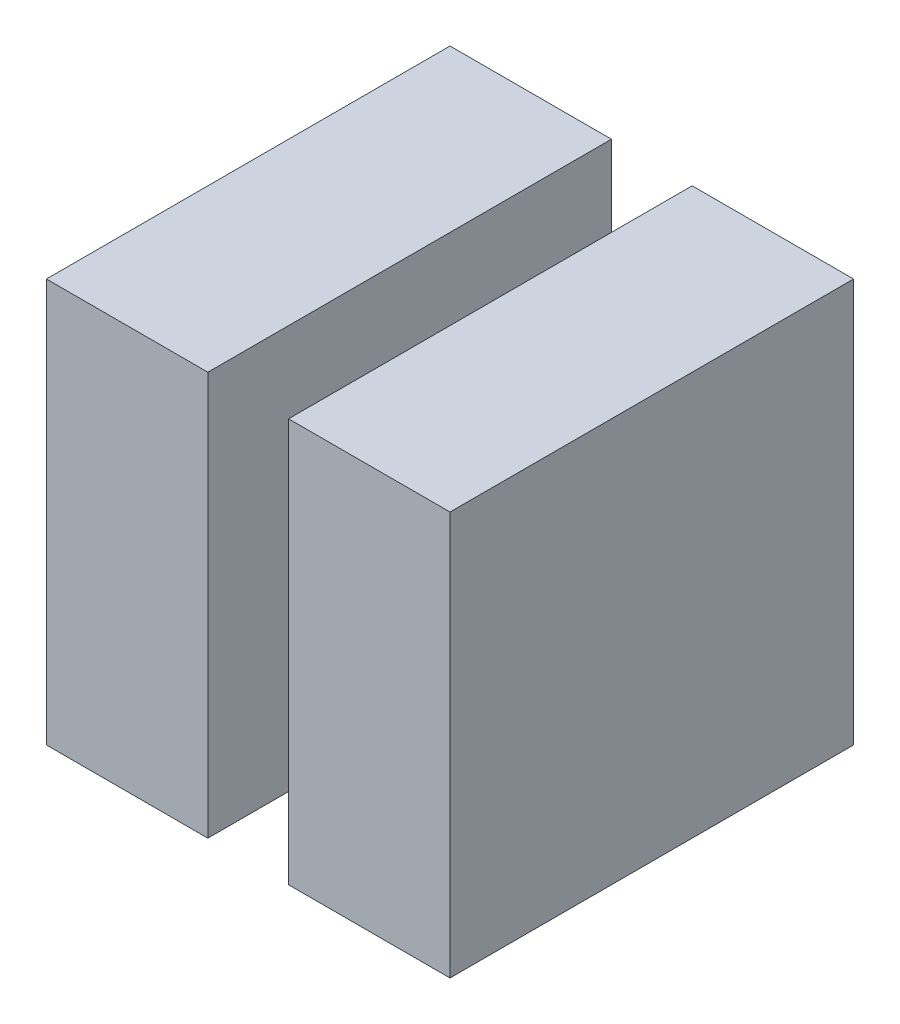
SolidWorks part; units mm, degrees
ref_plane "Płaszczyzna przednia" through (0, 0, 0) normal (0, 0, 1) x (1, 0, 0)
ref_plane "Płaszczyzna górna" through (0, 0, 0) normal (0, 1, 0) x (1, 0, 0)
ref_plane "Płaszczyzna prawa" through (0, 0, 0) normal (1, 0, 0) x (0, 0, -1)
sketch "Szkic1" plane through (0, 0, 0) normal (0, 0, 1) x (1, 0, 0)
  line L1 (0, 0) -> (20, 0)
  line L2 (0, 0) -> (0, 50)
  line L3 (0, 50) -> (20, 50)
  line L4 (20, 0) -> (20, 50)
  dimension "D1" = 20
  dimension "D2" = 50
extrude "Dodanie-wyciągnięcie1" add sketch "Szkic1" along normal blind 50
pattern_linear "Szyk liniowy1" count 2 spacing 30 along (1, 0, 0) of "Dodanie-wyciągnięcie1"
